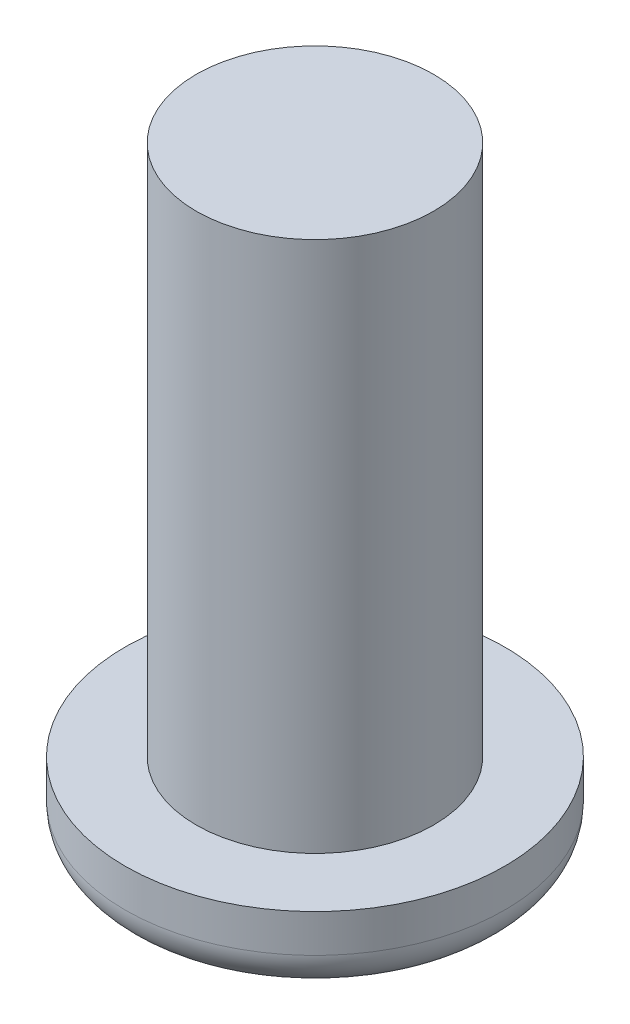
SolidWorks part; units mm, degrees
ref_plane "Front Plane" through (0, 0, 0) normal (0, 0, 1) x (1, 0, 0)
ref_plane "Top Plane" through (0, 0, 0) normal (0, 1, 0) x (1, 0, 0)
ref_plane "Right Plane" through (0, 0, 0) normal (1, 0, 0) x (0, 0, -1)
sketch "Sketch1" plane through (0, 0, 0) normal (0, 1, 0) x (1, 0, 0)
  circle A0 centre (0, 0) radius 6.35
  dimension "D1" = 12.7
extrude "Boss-Extrude1" add sketch "Sketch1" along normal blind 2.54
sketch "Sketch2" plane through (0, 2.54, 0) normal (0, 1, 0) x (1, 0, 0)
  circle A0 centre (0, 0) radius 3.9688
  dimension "D1" = 7.9375
fillet "Fillet2" radius 1.27 1 edges at (0, 0, 6.35)
extrude "Boss-Extrude3" add sketch "Sketch2" along normal blind 17.78
